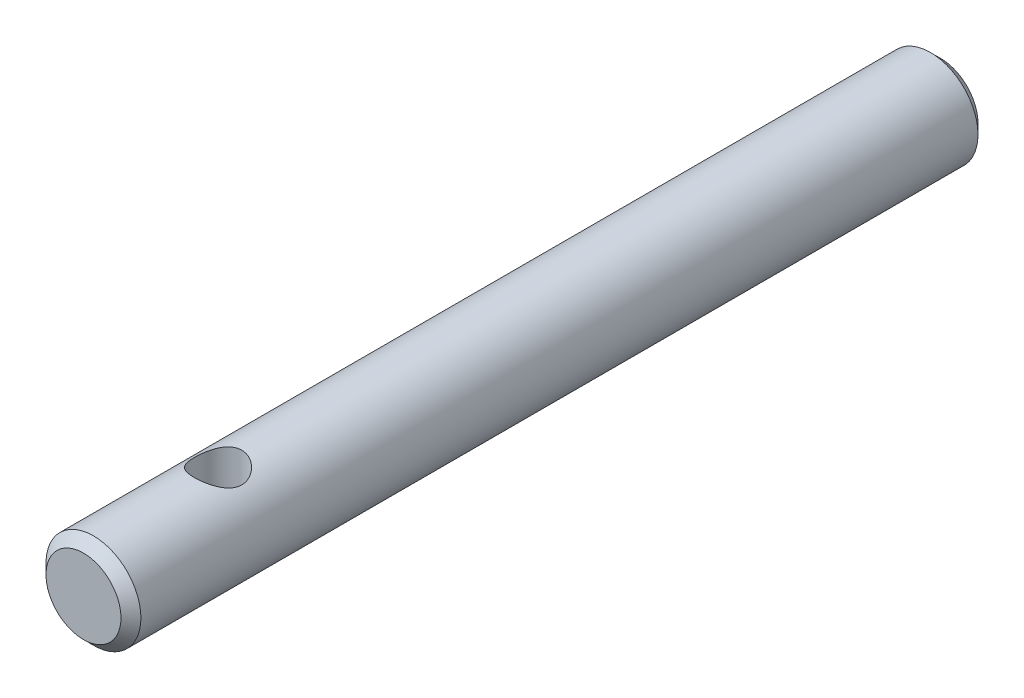
SolidWorks part; units mm, degrees
ref_plane "Front Plane" through (0, 0, 0) normal (0, 0, 1) x (1, 0, 0)
ref_plane "Top Plane" through (0, 0, 0) normal (0, 1, 0) x (1, 0, 0)
ref_plane "Right Plane" through (0, 0, 0) normal (1, 0, 0) x (0, 0, -1)
sketch "Sketch1" plane through (0, 0, 0) normal (0, 0, 1) x (1, 0, 0)
  circle A0 centre (0, 0) radius 2.3813
  dimension "D1" = 4.7625
extrude "Boss-Extrude1" add sketch "Sketch1" against normal blind 43
sketch "Sketch2" plane through (0, 0, 0) normal (0, 1, 0) x (1, 0, 0)
  line L0 (0, 0) -> (0, 43) construction
  line L1 (2.3813, 43) -> (-2.3813, 43) construction
  line L2 (-2.3813, 0) -> (2.3813, 0) construction
  circle A0 centre (0, 6.75) radius 1.1906
  dimension "D1" = 2.3813
  dimension "D2" = 6.75
extrude "Cut-Extrude1" cut sketch "Sketch2" against normal through all both and the other way through all
chamfer "Chamfer1" distance 0.5 angle 45 2 edges at (2.3813, 0, -43) (2.3813, 0, 0)
